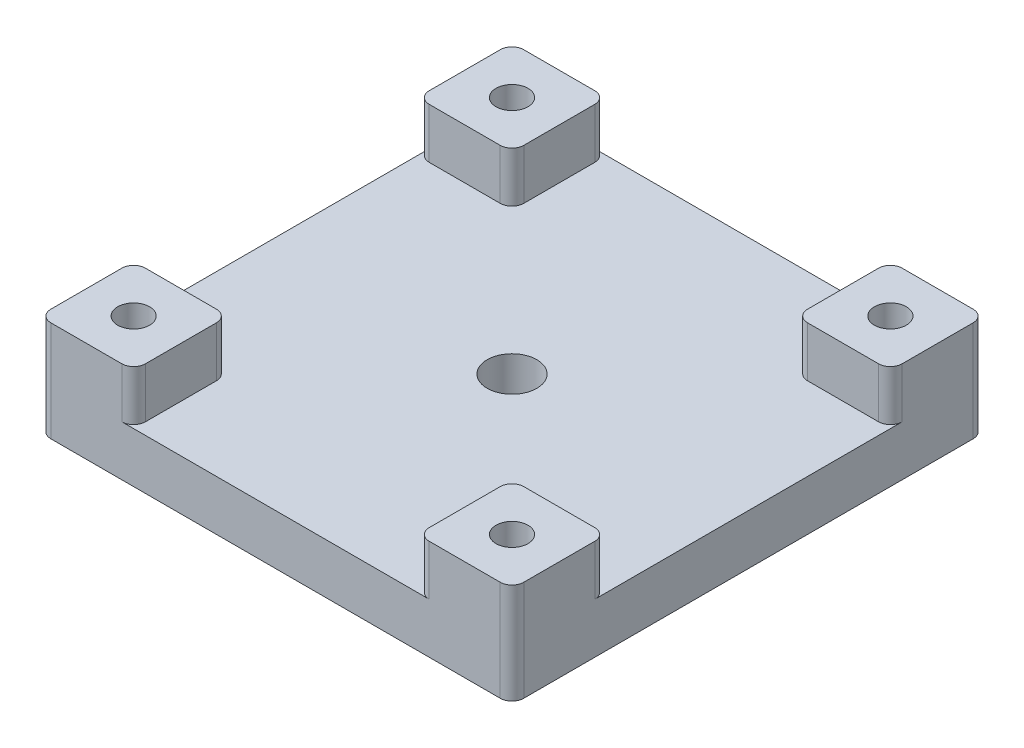
SolidWorks part; units mm, degrees
ref_plane "Front Plane" through (0, 0, 0) normal (0, 0, 1) x (1, 0, 0)
ref_plane "Top Plane" through (0, 0, 0) normal (0, 1, 0) x (1, 0, 0)
ref_plane "Right Plane" through (0, 0, 0) normal (1, 0, 0) x (0, 0, -1)
sketch "Sketch1" plane through (0, 0, 0) normal (0, 1, 0) x (1, 0, 0)
  line L1 (0, 0) -> (40, 0)
  line L2 (0, 0) -> (0, 40)
  line L3 (0, 40) -> (40, 40)
  line L4 (40, 0) -> (40, 40)
  dimension "D1" = 40
  dimension "D2" = 40
extrude "Boss-Extrude1" add sketch "Sketch1" along normal blind 8.5
sketch "Sketch2" plane through (0, 8.5, 0) normal (0, 1, 0) x (1, 0, 0)
  line L0 (0, 40) -> (0, 0) construction
  line L1 (0, 0) -> (40, 0) construction
  line L2 (40, 40) -> (0, 40) construction
  circle A0 centre (4, 4) radius 1.3525
  circle A1 centre (36, 4) radius 1.3525
  circle A2 centre (36, 36) radius 1.3525
  circle A3 centre (4, 36) radius 1.3525
  circle A4 centre (20, 20) radius 2.1
  dimension "D1" = 2.705
  dimension "D6" = 20
  dimension "D7" = 20
  dimension "D8" = 4.2
  dimension "D2" = 4
  dimension "D3" = 4
  dimension "D4" = 2
  dimension "D5" = 2
extrude "Cut-Extrude1" cut sketch "Sketch2" against normal through all
sketch "Sketch3" plane through (0, 8.5, 0) normal (0, 1, 0) x (1, 0, 0)
  line L0 (0, 40) -> (0, 0) construction
  line L1 (40, 40) -> (0, 40) construction
  circle A0 centre (20, 20) radius 3.5
  dimension "D1" = 20
  dimension "D3" = 7
  dimension "D2" = 20
extrude "Cut-Extrude2" cut sketch "Sketch3" against normal blind 4.25
sketch "Sketch4" plane through (0, 8.5, 0) normal (0, 1, 0) x (1, 0, 0)
  line L0 (0, 40) -> (0, 0) construction
  line L1 (0, 8) -> (8, 8)
  line L2 (0, 8) -> (0, 32)
  line L3 (0, 32) -> (8, 32)
  line L4 (40, 8) -> (40, 32)
  line L5 (40, 0) -> (40, 40) construction
  line L6 (40, 40) -> (0, 40) construction
  line L7 (8, 40) -> (32, 40)
  line L8 (8, 40) -> (8, 32)
  line L9 (8, 0) -> (32, 0)
  line L10 (32, 40) -> (32, 32)
  line L11 (0, 0) -> (40, 0) construction
  line L12 (32, 8) -> (32, 0)
  line L13 (32, 32) -> (40, 32)
  line L14 (8, 8) -> (8, 0)
  line L15 (32, 8) -> (40, 8)
  dimension "D1" = 8
extrude "Cut-Extrude3" cut sketch "Sketch4" against normal up to surface (4.25 mm away) up to face at (20, 4.25, -16.5)
fillet "Fillet1" radius 1 16 edges at (40, 6.375, -8) (32, 6.375, -8) (32, 6.375, 0) (40, 4.25, 0) (40, 6.375, -32) (32, 6.375, -32) (40, 4.25, -40) (32, 6.375, -40) (0, 4.25, -40) (8, 6.375, -40) (8, 6.375, -32) (0, 6.375, -32) (0, 6.375, -8) (0, 4.25, 0) (8, 6.375, -8) (8, 6.375, 0)
